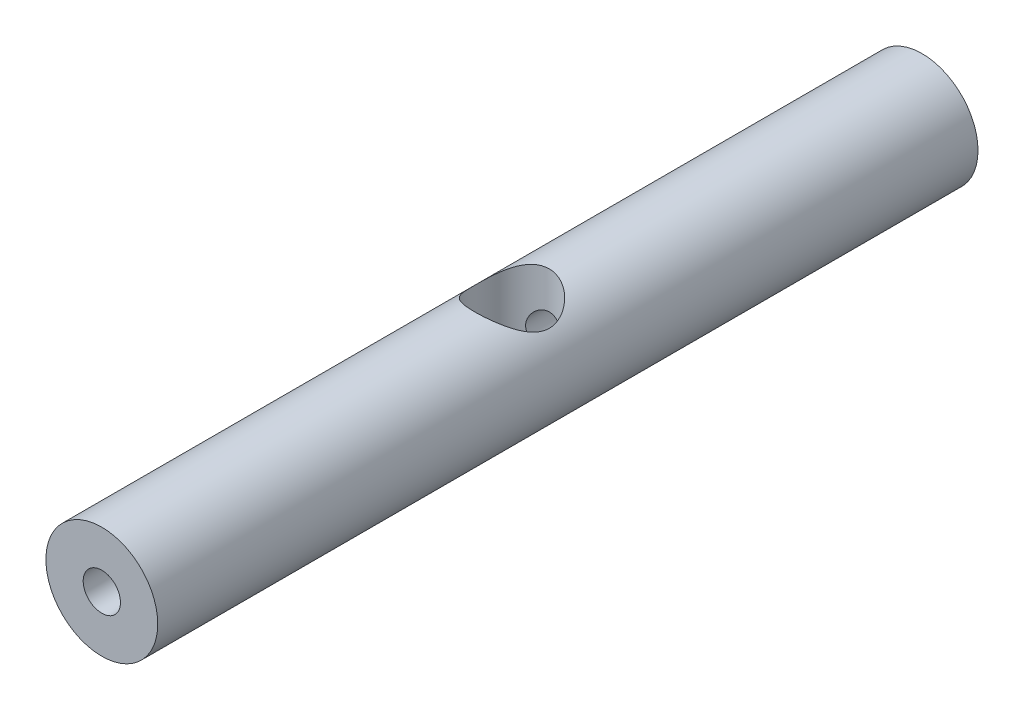
SolidWorks part; units mm, degrees
ref_plane "Front Plane" through (0, 0, 0) normal (0, 0, 1) x (1, 0, 0)
ref_plane "Top Plane" through (0, 0, 0) normal (0, 1, 0) x (1, 0, 0)
ref_plane "Right Plane" through (0, 0, 0) normal (1, 0, 0) x (0, 0, -1)
sketch "Sketch1" plane through (0, 0, 0) normal (0, 0, 1) x (1, 0, 0)
  circle A0 centre (0, 0) radius 9
  circle A1 centre (0, 0) radius 3
  dimension "D1" = 18
  dimension "D2" = 6
extrude "Boss-Extrude1" add sketch "Sketch1" along normal blind 132
sketch "Sketch2" plane through (0, 0, 0) normal (0, 1, 0) x (1, 0, 0)
  line L0 (0, 0) -> (0, -132) construction
  line L1 (-9, -132) -> (9, -132) construction
  circle A0 centre (0, -66) radius 6
  dimension "D1" = 12
extrude "Cut-Extrude1" cut sketch "Sketch2" against normal through all both and the other way through all
